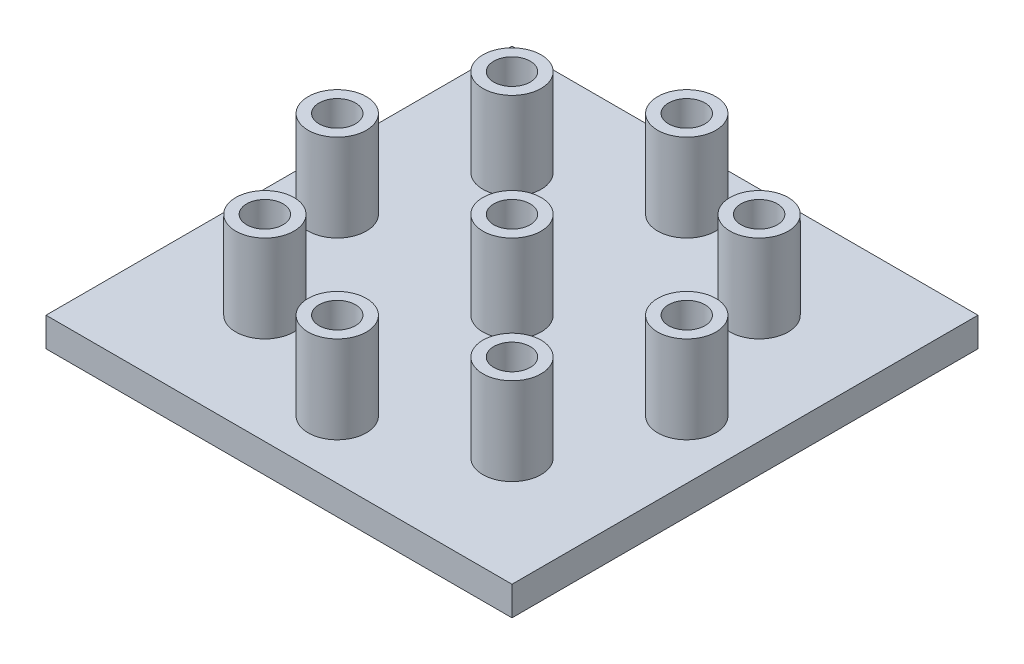
SolidWorks part; units mm, degrees
ref_plane "Front Plane" through (0, 0, 0) normal (0, 0, 1) x (1, 0, 0)
ref_plane "Top Plane" through (0, 0, 0) normal (0, 1, 0) x (1, 0, 0)
ref_plane "Right Plane" through (0, 0, 0) normal (1, 0, 0) x (0, 0, -1)
sketch "Sketch1" plane through (0, 0, 0) normal (0, 1, 0) x (1, 0, 0)
  line L1 (-25.4, -25.4) -> (25.4, -25.4)
  line L2 (-25.4, -25.4) -> (-25.4, 25.4)
  line L3 (-25.4, 25.4) -> (25.4, 25.4)
  line L4 (25.4, -25.4) -> (25.4, 25.4)
  line L5 (-25.4, -25.4) -> (25.4, 25.4) construction
  line L6 (-25.4, 25.4) -> (25.4, -25.4) construction
  point P0 (0, 0)
  dimension "D1" = 50.8
  dimension "D2" = 50.8
extrude "Boss-Extrude1" add sketch "Sketch1" along normal blind 3.175
sketch "Sketch2" plane through (0, 3.175, 0) normal (0, 1, 0) x (1, 0, 0)
  circle A0 centre (0, 0) radius 19.05 construction
  circle A1 centre (0, 19.05) radius 3.175
  circle A2 centre (13.4704, 13.4704) radius 3.175
  circle A3 centre (19.05, 0) radius 3.175
  circle A4 centre (13.4704, -13.4704) radius 3.175
  circle A5 centre (0, -19.05) radius 3.175
  circle A6 centre (-13.4704, -13.4704) radius 3.175
  circle A7 centre (-19.05, 0) radius 3.175
  circle A8 centre (-13.4704, 13.4704) radius 3.175
  circle A9 centre (0, 0) radius 3.175
  point P22 (0, 0)
  dimension "D1" = 38.1
  dimension "D3" = 6.35
  dimension "D4" = 19.05
  dimension "D5" = 19.05
  dimension "D2" = 8
extrude "Boss-Extrude2" add sketch "Sketch2" along normal blind 9.525
sketch "Sketch3" plane through (0, 12.7, 0) normal (0, 1, 0) x (1, 0, 0)
  circle A0 centre (0, 0) radius 19.05 construction
  circle A1 centre (0, 19.05) radius 1.9837
  circle A2 centre (13.4704, 13.4704) radius 1.9837
  circle A3 centre (19.05, 0) radius 1.9837
  circle A4 centre (13.4704, -13.4704) radius 1.9837
  circle A5 centre (0, -19.05) radius 1.9837
  circle A6 centre (-13.4704, -13.4704) radius 1.9837
  circle A7 centre (-19.05, 0) radius 1.9837
  circle A8 centre (-13.4704, 13.4704) radius 1.9837
  circle A9 centre (0, 0) radius 1.9837
  point P22 (0, 0)
  dimension "D4" = 3.9675
  dimension "D3" = 19.05
  dimension "D2" = 19.05
  dimension "D1" = 8
extrude "Cut-Extrude1" cut sketch "Sketch3" against normal through all
